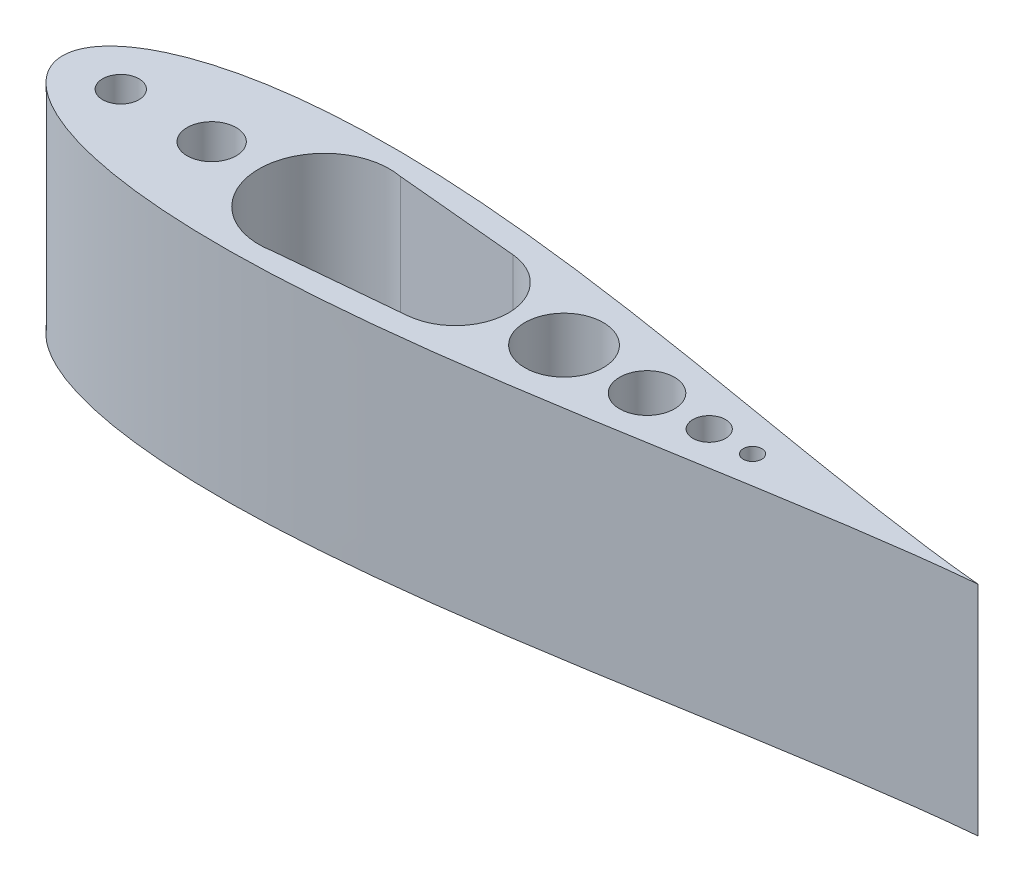
SolidWorks part; units mm, degrees
material "Polyurethane Foam Rigid"
ref_plane "Front Plane" through (0, 0, 0) normal (0, 0, 1) x (1, 0, 0)
ref_plane "Top Plane" through (0, 0, 0) normal (0, 1, 0) x (1, 0, 0)
ref_plane "Right Plane" through (0, 0, 0) normal (1, 0, 0) x (0, 0, -1)
sketch "Sketch1" plane through (0, 0, 0) normal (0, 1, 0) x (1, 0, 0)
  line L16 (-97.1704, 0) -> (-106.483, 0)
  line L17 (-45.5408, 15.24) -> (-13.8473, 12.2851)
  line L18 (-71.7704, 0) -> (-71.7704, -18.7053)
  line L19 (-55, 0) -> (55, 0) construction
  line L20 (-45.5408, -15.24) -> (-13.8473, -12.2851)
  line L21 (-71.7704, 0) -> (10.3102, 0)
  circle A1 centre (54.2104, 0) radius 2.159
  circle A2 centre (44.1263, 0) radius 3.81
  circle A3 centre (29.6435, 0) radius 6.3923
  circle A4 centre (10.3102, 0) radius 9.131
  arc A5 (-13.8473, -12.2851) -> (-13.8473, 12.2851) centre (-14.9927, 0) ccw
  arc A6 (-42.7236, 14.9773) -> (-42.7236, -14.9773) centre (-45.5408, 0) ccw
  circle A7 centre (-71.7704, 0) radius 5.715
  circle A8 centre (-92.9371, 0) radius 4.2333
  spline S0 degree 3 poles (-106.483, 0) (-106.482, -0.3362) (-106.4279, -1.1725) (-106.106, -2.6431) (-105.314, -4.4752) (-103.8975, -6.5043) (-101.808, -8.5717) (-99.0667, -10.5676) (-95.7198, -12.4267) (-91.8173, -14.1114) (-87.4067, -15.5993) (-82.5319, -16.8771) (-77.2341, -17.9374) (-71.5526, -18.7767) (-65.5251, -19.3955) (-59.1886, -19.7966) (-52.5791, -19.9863) (-45.732, -19.9729) (-38.6824, -19.7673) (-31.4645, -19.3826) (-24.1123, -18.8333) (-16.6591, -18.136) (-9.1376, -17.3083) (-1.5801, -16.3689) (5.9818, -15.3372) (13.5169, -14.233) (20.9946, -13.0761) (28.385, -11.8862) (35.6583, -10.6823) (42.7857, -9.4828) (49.7386, -8.3046) (56.4893, -7.1638) (63.0103, -6.0744) (69.2751, -5.0488) (75.2578, -4.0977) (80.9333, -3.2293) (86.2777, -2.4498) (91.2676, -1.7633) (95.8816, -1.1712) (100.0981, -0.6731) (103.6732, -0.2905) (105.8361, -0.0817) (106.7334, 0) knots 0.5 0.5 0.5 0.5 0.502167 0.50539 0.509656 0.514948 0.521245 0.528521 0.536745 0.545881 0.555891 0.56673 0.578353 0.59071 0.603747 0.61741 0.631639 0.646374 0.661552 0.677107 0.692975 0.709086 0.725371 0.741762 0.758188 0.774579 0.790865 0.806976 0.822844 0.8384 0.853578 0.868314 0.882544 0.896207 0.909245 0.921603 0.933227 0.944068 0.95408 0.963219 0.971447 0.977251 0.977251 0.977251 0.977251
  spline S1 degree 3 poles (-106.483, 0) (-106.482, 0.3362) (-106.4279, 1.1725) (-106.106, 2.6431) (-105.314, 4.4752) (-103.8975, 6.5043) (-101.808, 8.5717) (-99.0667, 10.5676) (-95.7198, 12.4267) (-91.8173, 14.1114) (-87.4067, 15.5993) (-82.5319, 16.8771) (-77.2341, 17.9374) (-71.5526, 18.7767) (-65.5251, 19.3955) (-59.1886, 19.7966) (-52.5791, 19.9863) (-45.732, 19.9729) (-38.6824, 19.7673) (-31.4645, 19.3826) (-24.1123, 18.8333) (-16.6591, 18.136) (-9.1376, 17.3083) (-1.5801, 16.3689) (5.9818, 15.3372) (13.5169, 14.233) (20.9946, 13.0761) (28.385, 11.8862) (35.6583, 10.6823) (42.7857, 9.4828) (49.7386, 8.3046) (56.4893, 7.1638) (63.0103, 6.0744) (69.2751, 5.0488) (75.2578, 4.0977) (80.9333, 3.2293) (86.2777, 2.4498) (91.2676, 1.7633) (95.8816, 1.1712) (100.0981, 0.6731) (103.6732, 0.2905) (105.8361, 0.0817) (106.7334, 0) knots 0.5 0.5 0.5 0.5 0.502167 0.50539 0.509656 0.514948 0.521245 0.528521 0.536745 0.545881 0.555891 0.56673 0.578353 0.59071 0.603747 0.61741 0.631639 0.646374 0.661552 0.677107 0.692975 0.709086 0.725371 0.741762 0.758188 0.774579 0.790865 0.806976 0.822844 0.8384 0.853578 0.868314 0.882544 0.896207 0.909245 0.921603 0.933227 0.944068 0.95408 0.963219 0.971447 0.977251 0.977251 0.977251 0.977251
  dimension "D1" = 11.43
  dimension "D2" = 30.48
  dimension "D3" = 26.2296
extrude "Boss-Extrude1" add sketch "Sketch1" along normal blind 50.8
